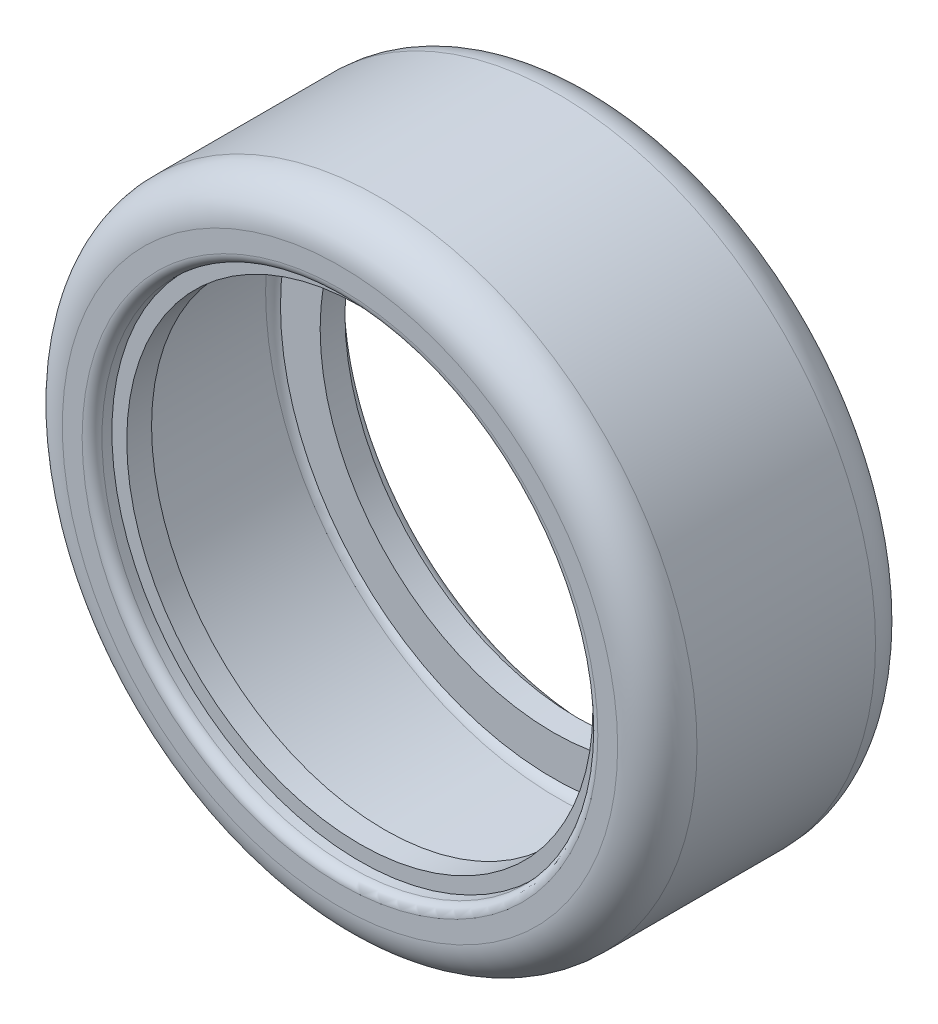
SolidWorks part; units mm, degrees
ref_plane "Plane1" through (0, 0, 0) normal (0, 0, 1) x (1, 0, 0)
ref_plane "Plane2" through (0, 0, 0) normal (0, 1, 0) x (1, 0, 0)
ref_plane "Plane3" through (0, 0, 0) normal (1, 0, 0) x (0, 0, -1)
sketch "Esquisse1" plane through (0, 0, 0) normal (0, 0, 1) x (1, 0, 0)
  circle A0 centre (0, 0) radius 23.5
  circle A1 centre (0, 0) radius 32
  dimension "D1" = 47
  dimension "D2" = 64
extrude "Base-Extrusion" add sketch "Esquisse1" along normal mid plane 26
fillet "Congé1" radius 4
sketch "Esquisse2" plane through (0, 0, 13) normal (0, 0, 1) x (1, 0, 0)
  circle A0 centre (0, 0) radius 25
  dimension "D1" = 50
extrude "Enlèv. mat.-Extru.1" cut sketch "Esquisse2" against normal blind 2
mirror "Symétrie1" about plane through (0, 0, 0) normal (0, 0, 1)
fillet "Congé2" radius 1
shell "Coque1" thickness 2.5
